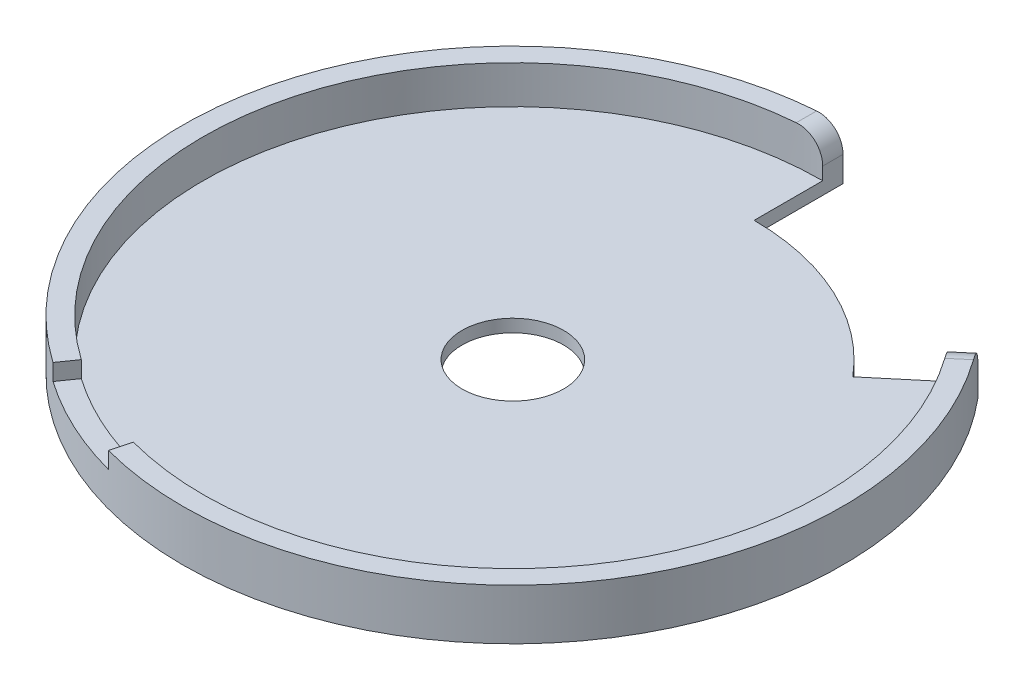
SolidWorks part; units mm, degrees
material "ASTM A36 Acero"
ref_plane "Alzado" through (0, 0, 0) normal (0, 0, 1) x (1, 0, 0)
ref_plane "Planta" through (0, 0, 0) normal (0, 1, 0) x (1, 0, 0)
ref_plane "Vista lateral" through (0, 0, 0) normal (1, 0, 0) x (0, 0, -1)
sketch "Croquis1" plane through (0, 0, 0) normal (0, 1, 0) x (1, 0, 0)
  circle A0 centre (0, 0) radius 260
  circle A1 centre (0, 0) radius 40
  dimension "D1" = 520
  dimension "D2" = 80
extrude "Saliente-Extruir1" add sketch "Croquis1" along normal blind 10
sketch "Croquis2" plane through (0, 10, 0) normal (0, 1, 0) x (1, 0, 0)
  circle A0 centre (0, 0) radius 244
  circle A1 centre (0, 0) radius 260
  circle A2 centre (0, 0) radius 260
  dimension "D2" = 488
  dimension "D1" = 0
extrude "Saliente-Extruir2" add sketch "Croquis2" along normal blind 30
sketch "Croquis3" plane through (0, 40, 0) normal (0, 1, 0) x (1, 0, 0)
  line L0 (0, 0) -> (199.1716, 167.1248)
  line L1 (0, 0) -> (0, 260)
  circle A0 centre (0, 0) radius 260
  circle A1 centre (0, 0) radius 190
  point P5 (109.8899, 235.6357)
  circle M2 centre (0, 0) radius 260
  circle M3 centre (0, 0) radius 244
  dimension "D1" = 520
  dimension "D2" = 380
  dimension "D3" = 50
extrude "Cortar-Extruir1" cut sketch "Croquis3" against normal through all contours A1 L0 L1 M3 | L1 L0 M3 M2
fillet "Redondeo1" radius 20 2 edges at (193.0432, 40, -161.9825) (0, 40, -252)
sketch "Croquis4" plane through (0, 40, 0) normal (0, 1, 0) x (1, 0, 0)
  line L0 (0, 0) -> (-109.8807, -235.64) construction
  line L1 (0, 0) -> (-260, 0) construction
  line L2 (0, 0) -> (-149.1299, -212.9795) construction
  line L3 (0, 0) -> (-67.293, -251.1407) construction
  line L4 (-139.9527, -199.8731) -> (-149.1299, -212.9795)
  line L5 (-63.1518, -235.6859) -> (-67.293, -251.1407)
  arc A0 (-20, 259.2296) -> (211.4372, 151.3087) centre (0, 0) ccw construction
  arc A1 (-149.1299, -212.9795) -> (-67.293, -251.1407) centre (0, 0) ccw
  arc A3 (-139.9527, -199.8731) -> (-63.1518, -235.6859) centre (0, 0) ccw
  dimension "D1" = 65
  dimension "D2" = 10
  dimension "D3" = 10
  dimension "D4" = 16
extrude "Cortar-Extruir2" cut sketch "Croquis4" against normal blind 13
